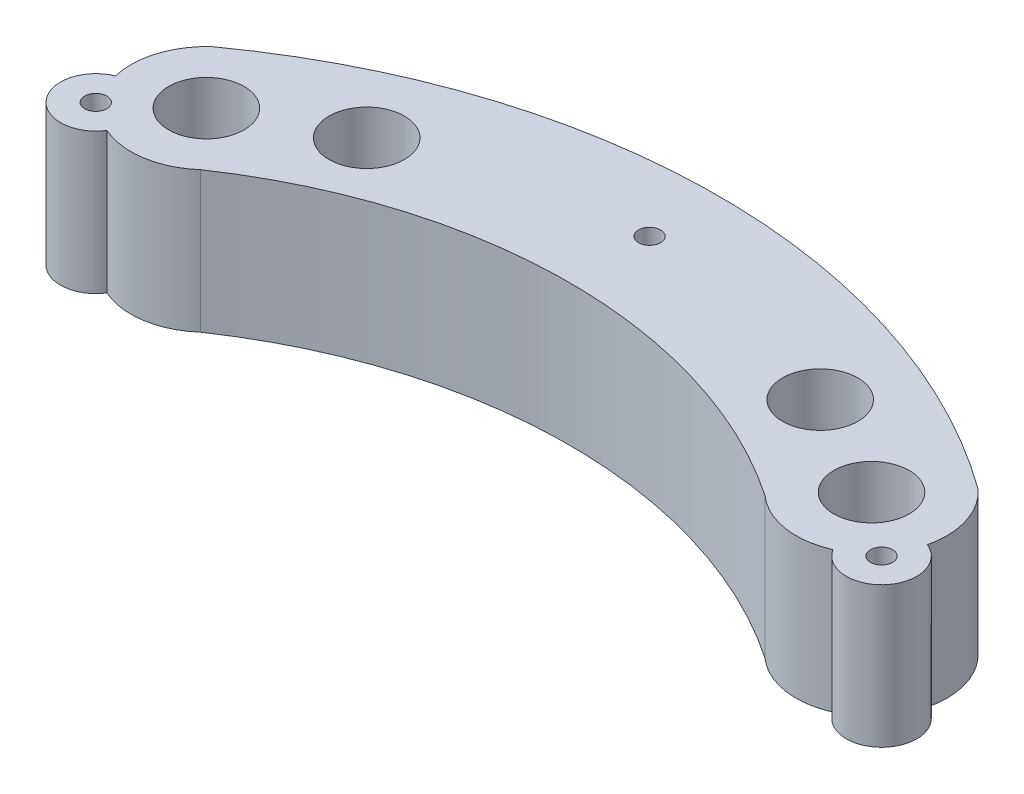
SolidWorks part; units mm, degrees
ref_plane "Front Plane" through (0, 0, 0) normal (0, 0, 1) x (1, 0, 0)
ref_plane "Top Plane" through (0, 0, 0) normal (0, 1, 0) x (1, 0, 0)
ref_plane "Right Plane" through (0, 0, 0) normal (1, 0, 0) x (0, 0, -1)
sketch "Sketch1" plane through (0, 0, 0) normal (0, 1, 0) x (1, 0, 0)
  circle A0 centre (0, 0) radius 4.7625
  circle A1 centre (13.3674, 6.8861) radius 4.7625
  circle A2 centre (70.647, 6.8861) radius 4.7625
  circle A3 centre (84.0144, 0) radius 4.7625
  point P8 (-116.7422, 41.4618)
  point P10 (70.647, 6.8861)
  point P11 (84.0144, 0)
  point P12 (84.0144, 0)
  point P13 (13.3674, 6.8861)
  point P14 (70.647, 6.8861)
  dimension "D1" = 6.8861
  dimension "D2" = 13.3674
  dimension "D3" = 57.2796
  dimension "D4" = 13.3674
  dimension "D5" = 6.8861
  dimension "D6" = 0
  dimension "D8" = 9.525
  dimension "D9" = 9.525
  dimension "D10" = 9.525
  dimension "D11" = 9.525
  dimension "D7" = 0
sketch "Sketch2" plane through (0, 0, 0) normal (0, 1, 0) x (1, 0, 0)
  circle A0 centre (0, 0) radius 9.525
  circle A1 centre (84.0144, 0) radius 9.525
  arc A2 (-6.35, 7.0995) -> (90.3644, 7.0995) centre (42.0072, -59.804) cw
  arc A3 (6.35, -7.0995) -> (77.6644, -7.0995) centre (42.0072, -59.643) cw
  dimension "D1" = 19.05
  dimension "D2" = 19.05
  dimension "D4" = 82.55
  dimension "D5" = 63.5
  dimension "D3" = 0
  dimension "D6" = 6.35
  dimension "D7" = 6.35
  dimension "D8" = 6.35
extrude "Boss-Extrude1" add sketch "Sketch2" along normal blind 14.605 and the other way blind 3.175 contours A0 A3 | A0 A3 A1 A2 | A1 A3
extrude "Cut-Extrude1" cut sketch "Sketch1" along normal blind 20.32
sketch "Sketch4" plane through (0, 0, 0) normal (0, 1, 0) x (1, 0, 0)
  circle A0 centre (13.3674, 6.8861) radius 2.2225
  circle A1 centre (0, 0) radius 2.2225
  circle A2 centre (70.647, 6.8861) radius 2.2225
  circle A3 centre (84.0144, 0) radius 2.2225
  dimension "D1" = 4.445
  dimension "D2" = 4.445
  dimension "D3" = 4.445
  dimension "D4" = 4.445
extrude "Cut-Extrude2" cut sketch "Sketch4" against normal blind 20.32
sketch "Sketch5" plane through (0, 14.605, 0) normal (0, 1, 0) x (1, 0, 0)
  circle A0 centre (-7.62, -6.35) radius 4.445
  circle A1 centre (91.6344, -6.35) radius 4.445
  circle A2 centre (84.0144, 0) radius 4.7625 construction
  dimension "D1" = 8.89
  dimension "D2" = 8.89
  dimension "D3" = 6.35
  dimension "D4" = 7.62
  dimension "D5" = 7.62
  dimension "D6" = 6.35
extrude "Boss-Extrude2" add sketch "Sketch5" against normal blind 17.78
sketch "Sketch6" plane through (0, 14.605, 0) normal (0, 1, 0) x (1, 0, 0)
  circle A0 centre (42.0072, 13.97) radius 1.397
  circle A1 centre (-7.62, -6.35) radius 1.397
  circle A2 centre (91.6344, -6.35) radius 1.397
  arc A4 (90.3644, 7.0995) -> (-6.35, 7.0995) centre (42.0072, -59.804) ccw construction
  dimension "D1" = 2.794
  dimension "D2" = 2.794
  dimension "D3" = 2.794
  dimension "D4" = 0
  dimension "D5" = 20.32
extrude "Cut-Extrude3" cut sketch "Sketch6" against normal blind 17.78
